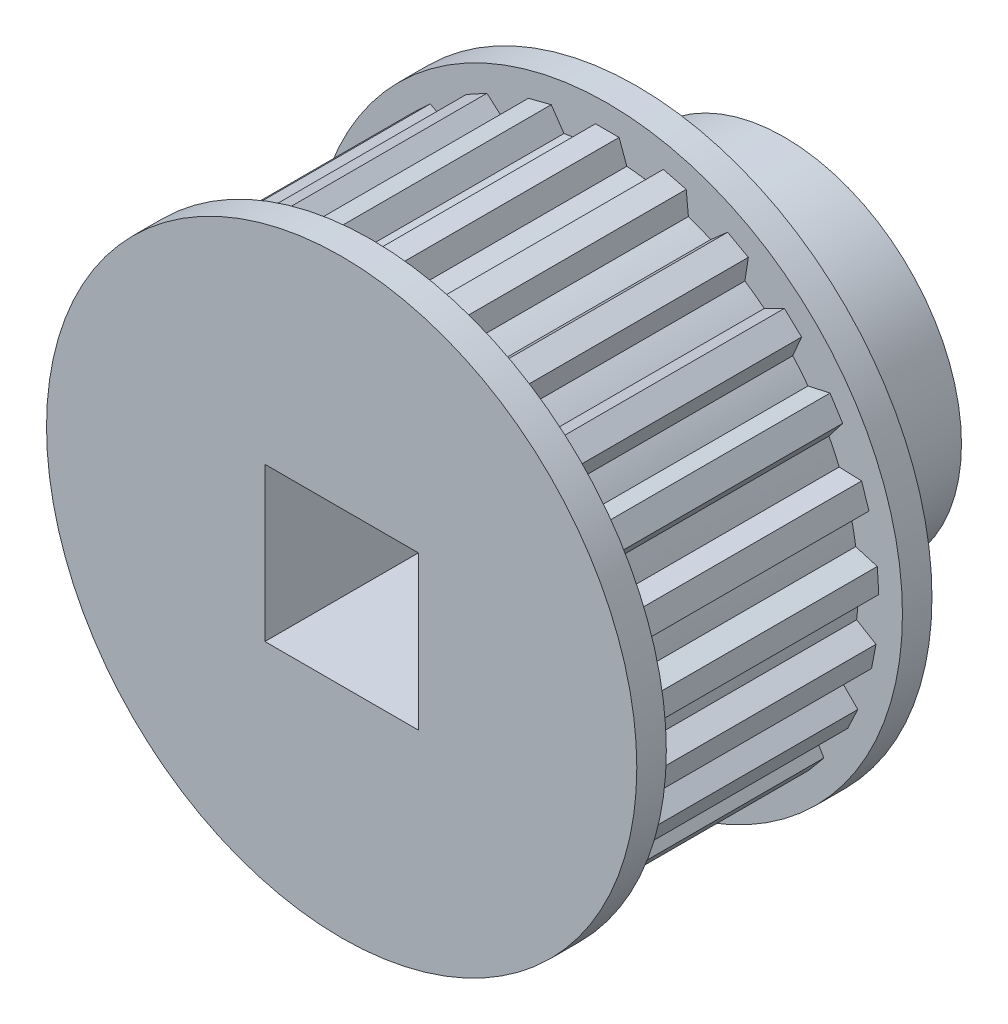
SolidWorks part; units mm, degrees
ref_plane "Front Plane" through (0, 0, 0) normal (0, 0, 1) x (1, 0, 0)
ref_plane "Top Plane" through (0, 0, 0) normal (0, 1, 0) x (1, 0, 0)
ref_plane "Right Plane" through (0, 0, 0) normal (1, 0, 0) x (0, 0, -1)
sketch "Sketch1" plane through (0, 0, 0) normal (0, 0, 1) x (1, 0, 0)
  line L0 (-0.4, 9.1913) -> (-0.661, 8.4743)
  line L1 (-0.4, 9.1913) -> (0.4, 9.1913)
  line L2 (0.4, 9.1913) -> (0.661, 8.4743)
  line L3 (0, 9.2) -> (0, -9.2) construction
  line L4 (1.8984, 9.002) -> (1.4672, 8.3724)
  line L5 (1.8984, 9.002) -> (2.6732, 8.8031)
  line L6 (2.6732, 8.8031) -> (2.7477, 8.0436)
  line L7 (4.0774, 8.2471) -> (3.5033, 7.7445)
  line L8 (4.0774, 8.2471) -> (4.7785, 7.8617)
  line L9 (4.7785, 7.8617) -> (4.6617, 7.1076)
  line L10 (6.0003, 6.974) -> (5.3192, 6.6299)
  line L11 (6.0003, 6.974) -> (6.5835, 6.4264)
  line L12 (6.5835, 6.4264) -> (6.2829, 5.725)
  line L13 (7.5461, 5.2627) -> (6.8009, 5.0988)
  line L14 (7.5461, 5.2627) -> (7.9748, 4.5872)
  line L15 (7.9748, 4.5872) -> (7.5092, 3.9827)
  line L16 (8.6178, 3.2207) -> (7.8552, 3.2473)
  line L17 (8.6178, 3.2207) -> (8.8651, 2.4598)
  line L18 (8.8651, 2.4598) -> (8.2638, 1.9901)
  line L19 (9.148, 0.9763) -> (8.416, 1.1918)
  line L20 (9.148, 0.9763) -> (9.1983, 0.1779)
  line L21 (9.1983, 0.1779) -> (8.499, -0.1276)
  line L22 (9.1034, -1.3294) -> (8.448, -0.9386)
  line L23 (9.1034, -1.3294) -> (8.9535, -2.1152)
  line L24 (8.9535, -2.1152) -> (8.2003, -2.2372)
  line L25 (8.4868, -3.5515) -> (7.9492, -3.0101)
  line L26 (8.4868, -3.5515) -> (8.1462, -4.2754)
  line L27 (8.1462, -4.2754) -> (7.3863, -4.2062)
  line L28 (7.337, -5.5505) -> (6.9509, -4.8924)
  line L29 (7.337, -5.5505) -> (6.827, -6.167)
  line L30 (6.827, -6.167) -> (6.1082, -5.911)
  line L31 (5.7261, -7.2008) -> (5.5158, -6.4673)
  line L32 (5.7261, -7.2008) -> (5.0789, -7.671)
  line L33 (5.0789, -7.671) -> (4.4463, -7.2443)
  line L34 (3.7555, -8.3986) -> (3.7341, -7.6358)
  line L35 (3.7555, -8.3986) -> (3.0116, -8.6931)
  line L36 (3.0116, -8.6931) -> (2.505, -8.1225)
  line L37 (1.5488, -9.0687) -> (1.7179, -8.3246)
  line L38 (1.5488, -9.0687) -> (0.7551, -9.169)
  line L39 (0.7551, -9.169) -> (0.4063, -8.4903)
  line L40 (-0.7551, -9.169) -> (-0.4063, -8.4903)
  line L41 (-0.7551, -9.169) -> (-1.5488, -9.0687)
  line L42 (-1.5488, -9.0687) -> (-1.7179, -8.3246)
  line L43 (-3.0116, -8.6931) -> (-2.505, -8.1225)
  line L44 (-3.0116, -8.6931) -> (-3.7555, -8.3986)
  line L45 (-3.7555, -8.3986) -> (-3.7341, -7.6358)
  line L46 (-5.0789, -7.671) -> (-4.4463, -7.2443)
  line L47 (-5.0789, -7.671) -> (-5.7261, -7.2008)
  line L48 (-5.7261, -7.2008) -> (-5.5158, -6.4673)
  line L49 (-6.827, -6.167) -> (-6.1082, -5.911)
  line L50 (-6.827, -6.167) -> (-7.337, -5.5505)
  line L51 (-7.337, -5.5505) -> (-6.9509, -4.8924)
  line L52 (-8.1462, -4.2754) -> (-7.3863, -4.2062)
  line L53 (-8.1462, -4.2754) -> (-8.4868, -3.5515)
  line L54 (-8.4868, -3.5515) -> (-7.9492, -3.0101)
  line L55 (-8.9535, -2.1152) -> (-8.2003, -2.2372)
  line L56 (-8.9535, -2.1152) -> (-9.1034, -1.3294)
  line L57 (-9.1034, -1.3294) -> (-8.448, -0.9386)
  line L58 (-9.1983, 0.1779) -> (-8.499, -0.1276)
  line L59 (-9.1983, 0.1779) -> (-9.148, 0.9763)
  line L60 (-9.148, 0.9763) -> (-8.416, 1.1918)
  line L61 (-8.8651, 2.4598) -> (-8.2638, 1.9901)
  line L62 (-8.8651, 2.4598) -> (-8.6178, 3.2207)
  line L63 (-8.6178, 3.2207) -> (-7.8552, 3.2473)
  line L64 (-7.9748, 4.5872) -> (-7.5092, 3.9827)
  line L65 (-7.9748, 4.5872) -> (-7.5461, 5.2627)
  line L66 (-7.5461, 5.2627) -> (-6.8009, 5.0988)
  line L67 (-6.5835, 6.4264) -> (-6.2829, 5.725)
  line L68 (-6.5835, 6.4264) -> (-6.0003, 6.974)
  line L69 (-6.0003, 6.974) -> (-5.3192, 6.6299)
  line L70 (-4.7785, 7.8617) -> (-4.6617, 7.1076)
  line L71 (-4.7785, 7.8617) -> (-4.0774, 8.2471)
  line L72 (-4.0774, 8.2471) -> (-3.5033, 7.7445)
  line L73 (-2.6732, 8.8031) -> (-2.7477, 8.0436)
  line L74 (-2.6732, 8.8031) -> (-1.8984, 9.002)
  line L75 (-1.8984, 9.002) -> (-1.4672, 8.3724)
  arc A0 (1.4672, 8.3724) -> (0.661, 8.4743) centre (0, 0) ccw
  arc A2 (3.5033, 7.7445) -> (2.7477, 8.0436) centre (0, 0) ccw
  arc A3 (5.3192, 6.6299) -> (4.6617, 7.1076) centre (0, 0) ccw
  arc A4 (6.8009, 5.0988) -> (6.2829, 5.725) centre (0, 0) ccw
  arc A5 (7.8552, 3.2473) -> (7.5092, 3.9827) centre (0, 0) ccw
  arc A6 (8.416, 1.1918) -> (8.2638, 1.9901) centre (0, 0) ccw
  arc A7 (8.448, -0.9386) -> (8.499, -0.1276) centre (0, 0) ccw
  arc A8 (7.9492, -3.0101) -> (8.2003, -2.2372) centre (0, 0) ccw
  arc A9 (6.9509, -4.8924) -> (7.3863, -4.2062) centre (0, 0) ccw
  arc A10 (5.5158, -6.4673) -> (6.1082, -5.911) centre (0, 0) ccw
  arc A11 (3.7341, -7.6358) -> (4.4463, -7.2443) centre (0, 0) ccw
  arc A12 (1.7179, -8.3246) -> (2.505, -8.1225) centre (0, 0) ccw
  arc A13 (-0.4063, -8.4903) -> (0.4063, -8.4903) centre (0, 0) ccw
  arc A14 (-2.505, -8.1225) -> (-1.7179, -8.3246) centre (0, 0) ccw
  arc A15 (-4.4463, -7.2443) -> (-3.7341, -7.6358) centre (0, 0) ccw
  arc A16 (-6.1082, -5.911) -> (-5.5158, -6.4673) centre (0, 0) ccw
  arc A17 (-7.3863, -4.2062) -> (-6.9509, -4.8924) centre (0, 0) ccw
  arc A18 (-8.2003, -2.2372) -> (-7.9492, -3.0101) centre (0, 0) ccw
  arc A19 (-8.499, -0.1276) -> (-8.448, -0.9386) centre (0, 0) ccw
  arc A20 (-8.2638, 1.9901) -> (-8.416, 1.1918) centre (0, 0) ccw
  arc A21 (-7.5092, 3.9827) -> (-7.8552, 3.2473) centre (0, 0) ccw
  arc A22 (-6.2829, 5.725) -> (-6.8009, 5.0988) centre (0, 0) ccw
  arc A23 (-4.6617, 7.1076) -> (-5.3192, 6.6299) centre (0, 0) ccw
  arc A24 (-2.7477, 8.0436) -> (-3.5033, 7.7445) centre (0, 0) ccw
  arc A25 (-0.661, 8.4743) -> (-1.4672, 8.3724) centre (0, 0) ccw
  point P109 (0, 0)
  dimension "D1" = 17
  dimension "D3" = 0.8
  dimension "D4" = 40
  dimension "D5" = 25
extrude "Boss-Extrude1" add sketch "Sketch1" along normal mid plane 10
sketch "Sketch2" plane through (0, 0, 5) normal (0, 0, 1) x (1, 0, 0)
  circle A0 centre (0, 0) radius 10
  dimension "D1" = 20
extrude "Boss-Extrude2" add sketch "Sketch2" against normal blind 1
mirror "Mirror1" about plane through (0, 0, 0) normal (0, 0, 1) of "Boss-Extrude2"
sketch "Sketch4" plane through (0, 0, -5) normal (0, 0, -1) x (-1, 0, 0)
  circle A0 centre (0, 0) radius 6
  dimension "D1" = 12
extrude "Boss-Extrude3" add sketch "Sketch4" along normal blind 5
sketch "Sketch5" plane through (0, 0, 5) normal (0, 0, 1) x (1, 0, 0)
  line L1 (2.6, -2.6) -> (-2.6, -2.6)
  line L2 (2.6, -2.6) -> (2.6, 2.6)
  line L3 (2.6, 2.6) -> (-2.6, 2.6)
  line L4 (-2.6, -2.6) -> (-2.6, 2.6)
  line L5 (2.6, -2.6) -> (-2.6, 2.6) construction
  line L6 (2.6, 2.6) -> (-2.6, -2.6) construction
  point P0 (0, 0)
  dimension "D1" = 5.2
extrude "Cut-Extrude1" cut sketch "Sketch5" against normal up to next
equation "\"d1\"= 16"
